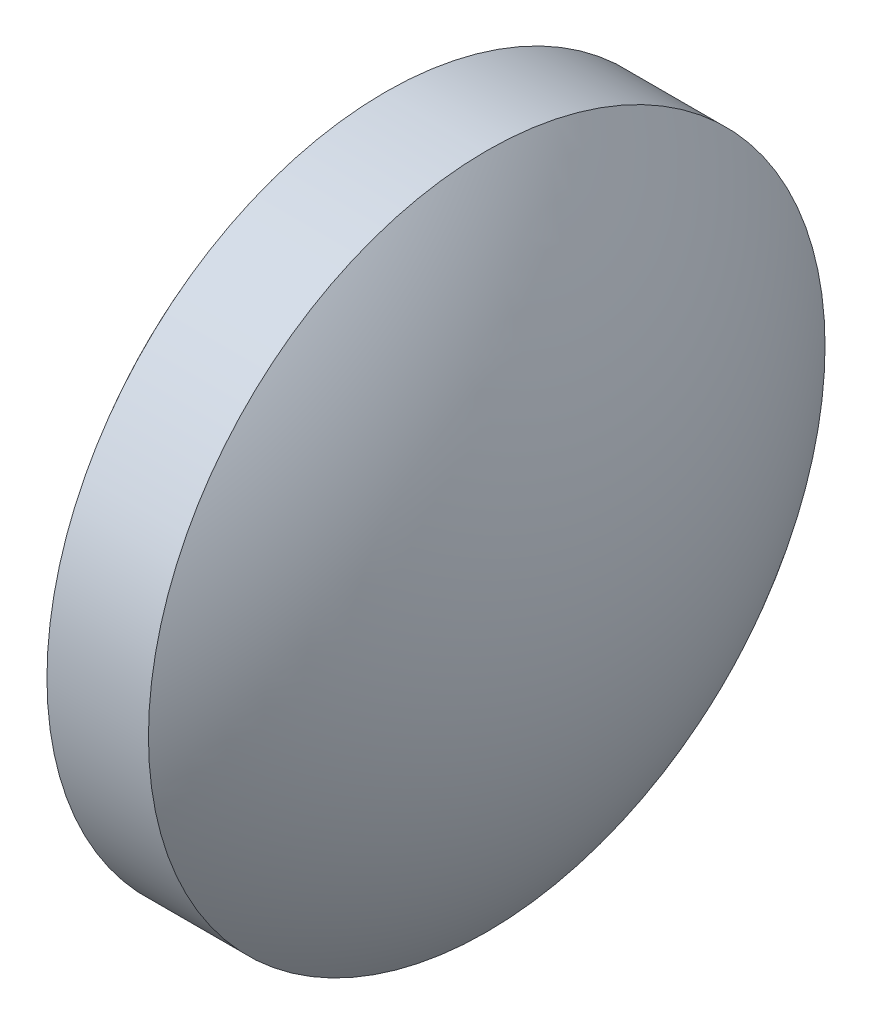
SolidWorks part; units mm, degrees
ref_plane "前视基准面" through (0, 0, 0) normal (0, 0, 1) x (1, 0, 0)
ref_plane "上视基准面" through (0, 0, 0) normal (0, 1, 0) x (1, 0, 0)
ref_plane "右视基准面" through (0, 0, 0) normal (1, 0, 0) x (0, 0, -1)
sketch "草图1" plane through (0, 0, 0) normal (0, 0, 1) x (1, 0, 0)
  line L0 (31.2226, 19.1402) -> (36.802, 19.1402) construction
  line L1 (33.2887, 24.1402) -> (34.7887, 24.1402)
  line L2 (34.7887, 24.1402) -> (34.7887, 14.1402)
  line L3 (34.7887, 14.1402) -> (33.2887, 14.1402)
  line L4 (33.2887, 14.1402) -> (33.2887, 24.1402)
  arc A0 (33.2887, 24.1402) -> (33.2887, 14.1402) centre (39.9637, 19.1402) ccw
  arc A1 (34.7887, 14.1402) -> (34.7887, 24.1402) centre (28.1137, 19.1402) ccw
  dimension "D1" = 10
  dimension "D2" = 1.5
revolve "旋转1" add sketch "草图1" angle 360 about L0
